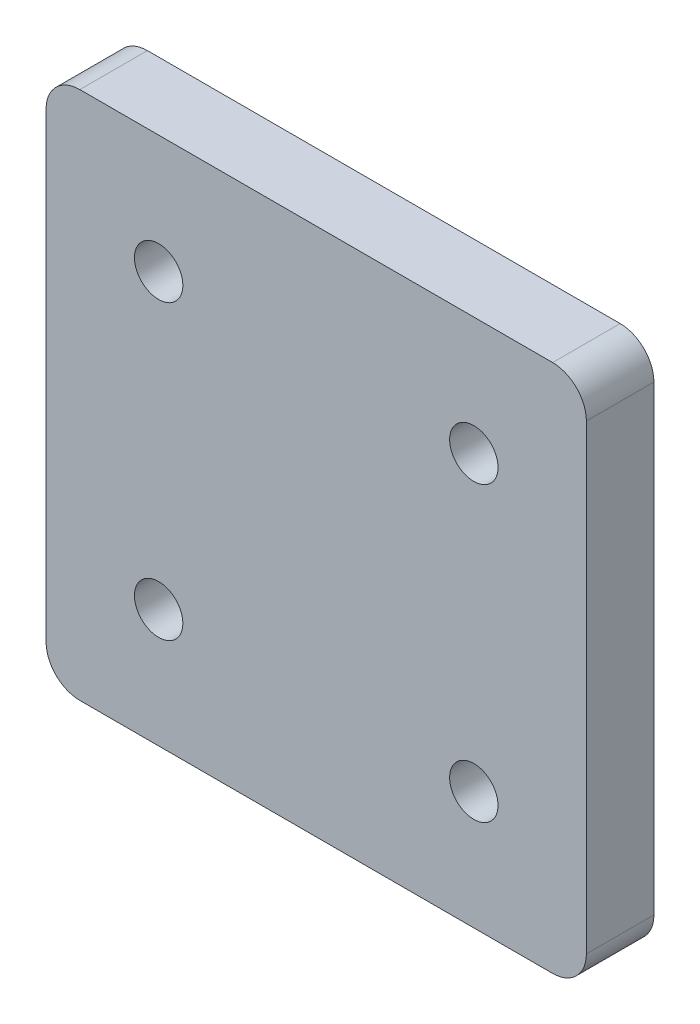
SolidWorks part; units mm, degrees
ref_plane "Front Plane" through (0, 0, 0) normal (0, 0, 1) x (1, 0, 0)
ref_plane "Top Plane" through (0, 0, 0) normal (0, 1, 0) x (1, 0, 0)
ref_plane "Right Plane" through (0, 0, 0) normal (1, 0, 0) x (0, 0, -1)
sketch "Sketch1" plane through (0, 0, 0) normal (0, 0, 1) x (1, 0, 0)
  line L0 (0, 0) -> (0, -39) construction
  line L2 (-20, -19.5) -> (20, -19.5) construction
  line L6 (-24, -43) -> (24, -43)
  line L7 (-24, -43) -> (-24, 4)
  line L8 (-24, 4) -> (24, 4)
  line L9 (24, -43) -> (24, 4)
  line L10 (-24, -43) -> (24, 4) construction
  line L11 (-24, 4) -> (24, -43) construction
  circle A6 centre (14, -32.5) radius 1.65
  circle A7 centre (-14, -32.5) radius 1.65
  circle A8 centre (-14, -6.5) radius 1.65
  circle A9 centre (14, -6.5) radius 1.65
  point P11 (0, -19.5)
extrude "Boss-Extrude1" add sketch "Sketch1" along normal blind 6
sketch "Sketch2" plane through (0, 0, 6) normal (0, 0, 1) x (1, 0, 0)
  circle A0 centre (-14, -6.5) radius 2.15
  circle A1 centre (14, -6.5) radius 2.15
  circle A2 centre (-14, -32.5) radius 2.15
  circle A3 centre (14, -32.5) radius 2.15
  dimension "D1" = 4.3
  dimension "D2" = 4.3
  dimension "D3" = 4.3
  dimension "D4" = 4.3
extrude "Cut-Extrude1" cut sketch "Sketch2" against normal through all
fillet "Fillet1" radius 3 4 edges at (24, -43, 3) (-24, 4, 3) (-24, -43, 3) (24, 4, 3)
